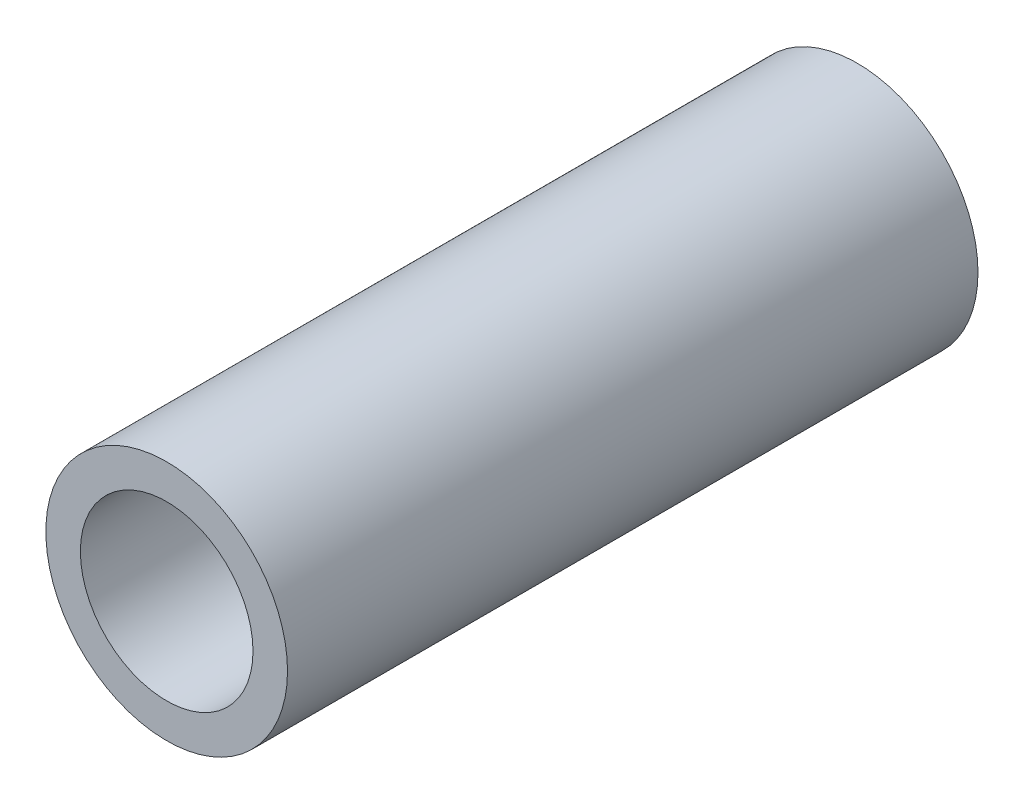
SolidWorks part; units mm, degrees
ref_plane "Front Plane" through (0, 0, 0) normal (0, 0, 1) x (1, 0, 0)
ref_plane "Top Plane" through (0, 0, 0) normal (0, 1, 0) x (1, 0, 0)
ref_plane "Right Plane" through (0, 0, 0) normal (1, 0, 0) x (0, 0, -1)
sketch "Sketch1" plane through (0, 0, 0) normal (0, 0, 1) x (1, 0, 0)
  circle A0 centre (0, 0) radius 6.35
  dimension "D1" = 12.7
extrude "Extrude-Thin1" add sketch "Sketch1" along normal blind 50.8 thin
sketch "Sketch2" plane through (0, 0, 0) normal (0, 0, -1) x (-1, 0, 0)
  circle A0 centre (0, 0) radius 6.35
  dimension "D1" = 12.7
extrude "Boss-Extrude1" add sketch "Sketch2" against normal blind 2.54
